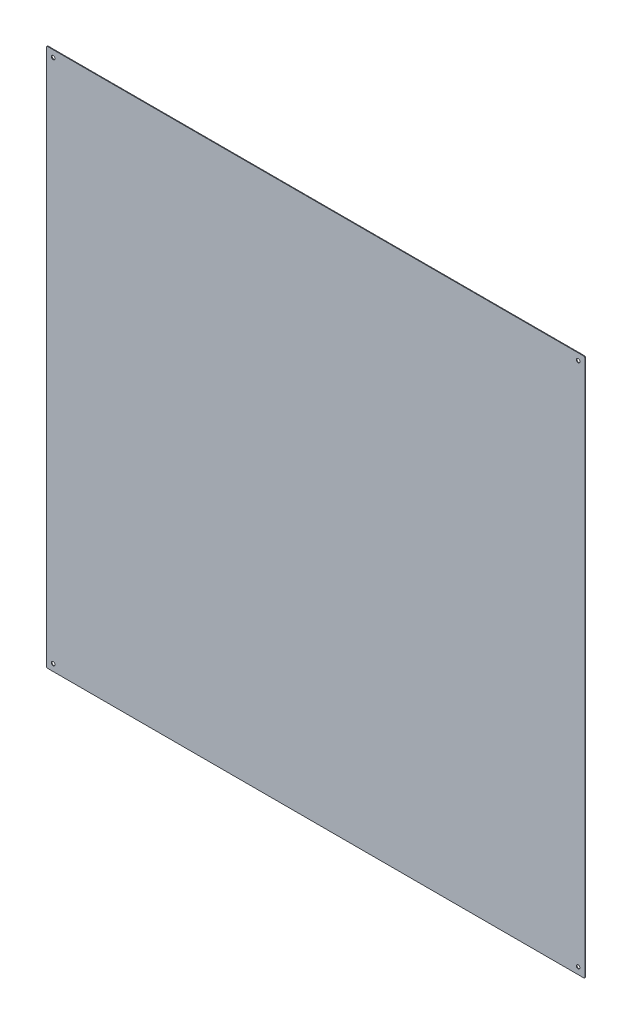
SolidWorks part; units mm, degrees
material "Plain Carbon Steel"
ref_plane "Front Plane" through (0, 0, 0) normal (0, 0, 1) x (1, 0, 0)
ref_plane "Top Plane" through (0, 0, 0) normal (0, 1, 0) x (1, 0, 0)
ref_plane "Right Plane" through (0, 0, 0) normal (1, 0, 0) x (0, 0, -1)
sketch "Sketch1" plane through (0, 0, 6) normal (0, 0, 1) x (1, 0, 0)
  line L1 (-602.5, 602.5) -> (602.5, 602.5)
  line L2 (-602.5, 602.5) -> (-602.5, -602.5)
  line L3 (-602.5, -602.5) -> (602.5, -602.5)
  line L4 (602.5, 602.5) -> (602.5, -602.5)
  line L5 (-602.5, 602.5) -> (602.5, -602.5) construction
  line L6 (-602.5, -602.5) -> (602.5, 602.5) construction
  point P0 (0, 0)
  dimension "D1" = 1205
extrude "Boss-Extrude1" add sketch "Sketch1" along normal blind 1.5
fillet "Fillet1" radius 3 4 edges at (-602.5, 602.5, 6.75) (602.5, 602.5, 6.75) (602.5, -602.5, 6.75) (-602.5, -602.5, 6.75)
sketch "Sketch2" plane through (0, 0, 6) normal (0, 0, -1) x (-1, 0, 0)
  circle A0 centre (587.3223, -587.3223) radius 4
  circle A1 centre (-587.3223, -587.3223) radius 4
  circle A2 centre (-587.3223, 587.3223) radius 4
  circle A3 centre (587.3223, 587.3223) radius 4
extrude "Cut-Extrude1" cut sketch "Sketch2" against normal through all
